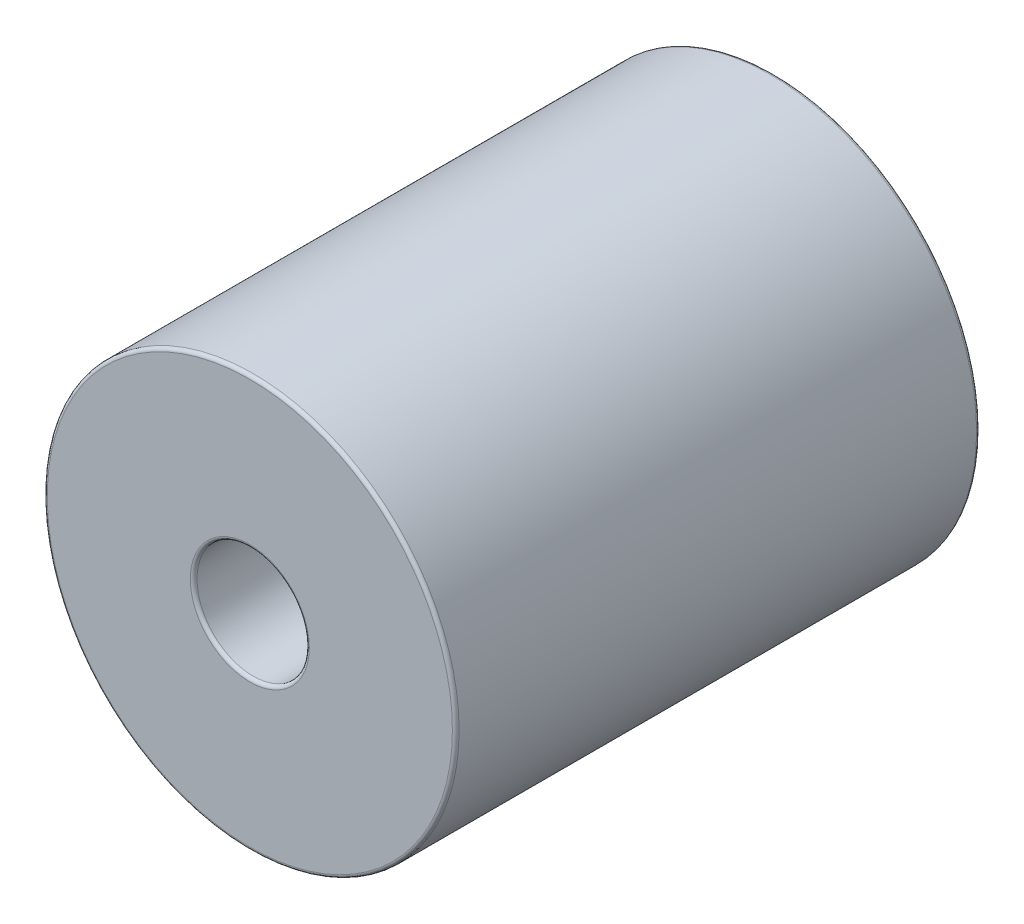
SolidWorks part; units mm, degrees
material "Copper"
ref_plane "Front" through (0, 0, 0) normal (0, 0, 1) x (1, 0, 0)
ref_plane "Top" through (0, 0, 0) normal (0, 1, 0) x (1, 0, 0)
ref_plane "Right" through (0, 0, 0) normal (1, 0, 0) x (0, 0, -1)
sketch "Sketch1" plane through (0, 0, 0) normal (0, 0, 1) x (1, 0, 0)
  line L0 (0, 0.5953) -> (0, -0.5953) construction
  line L1 (0, 2.1828) -> (0, -2.1828) construction
  line L2 (0, 1.9844) -> (0, -1.9844) construction
  circle A0 centre (0, 0) radius 1.9844 construction
  circle A1 centre (0, 0) radius 2.1828 construction
  dimension "od" = 4.3656
  dimension "compressed od" = 3.9688
  dimension "for wire rope dia" = 1.1906
sketch "Sketch2" plane through (0, 0, 0) normal (1, 0, 0) x (0, 0, -1)
  line L0 (-2.7781, 0) -> (2.7781, 0) construction
  dimension "sleeve lg" = 5.5562
sketch "Sketch3" plane through (0, 0, 0) normal (0, 0, 1) x (1, 0, 0)
  circle A0 centre (0, 0) radius 2.1828
  circle A1 centre (0, 0) radius 0.5953
extrude "Boss-Extrude1" add sketch "Sketch3" along normal up to vertex (2.7781 mm away) and the other way up to vertex (2.7781 mm away) up to point (0, 0, 2.7781) other way up to point (0, 0, -2.7781)
fillet "Fillet1" radius 0.0357 4 edges at (2.1828, 0, -2.7781) (2.1828, 0, 2.7781) (0.5953, 0, 2.7781) (0.5953, 0, -2.7781)
equation "\"D1@Fillet1\"=\"for wire rope dia@Sketch1\"*.03"
